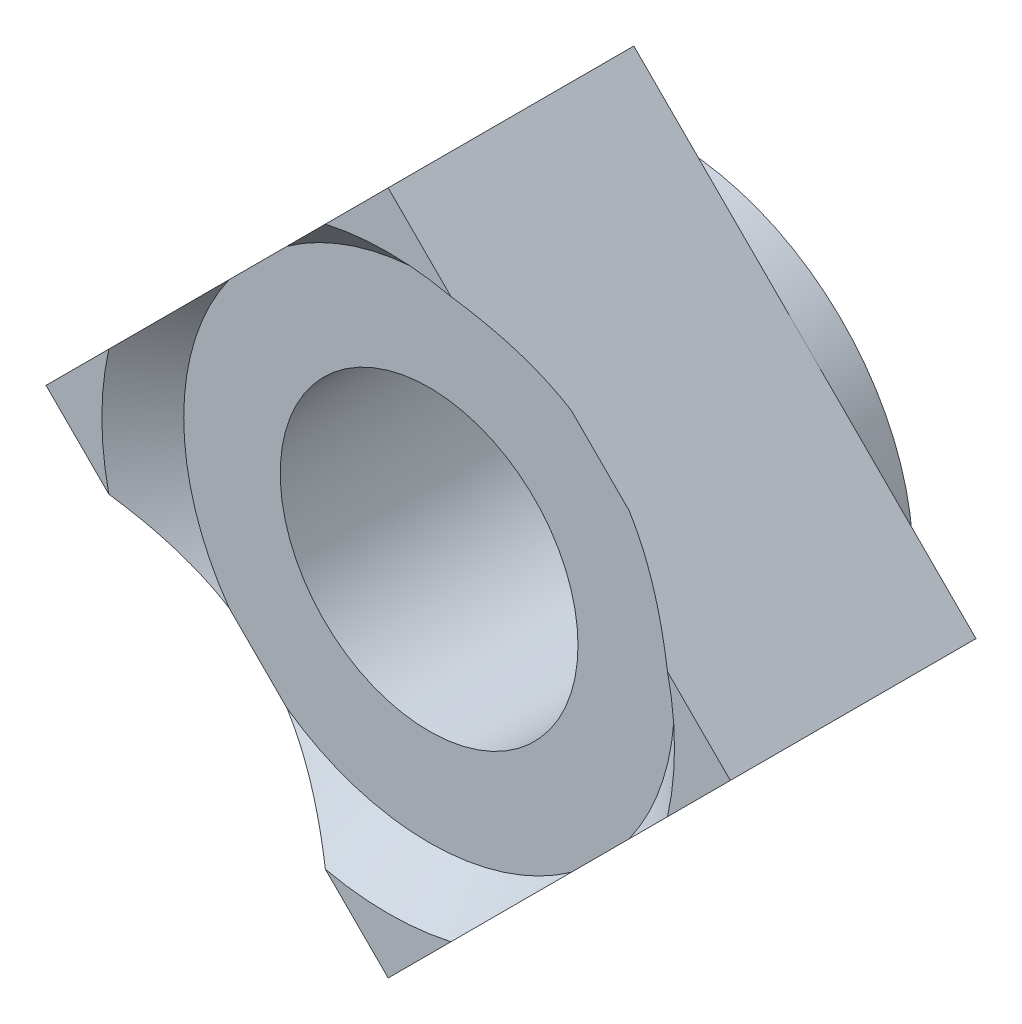
SolidWorks part; units mm, degrees
ref_plane "前视基准面" through (0, 0, 0) normal (0, 0, 1) x (1, 0, 0)
ref_plane "上视基准面" through (0, 0, 0) normal (0, 1, 0) x (1, 0, 0)
ref_plane "右视基准面" through (0, 0, 0) normal (1, 0, 0) x (0, 0, -1)
sketch "草图1" plane through (0, 0, 0) normal (0, 0, 1) x (1, 0, 0)
  circle A0 centre (0, 0) radius 6.5
  dimension "s" = 13
extrude "拉伸1" add sketch "草图1" along normal blind 1
sketch "草图2" plane through (0, 0, 1) normal (0, 0, 1) x (1, 0, 0)
  line L0 (0, 9.1924) -> (-9.1924, 0)
  line L1 (-9.1924, 0) -> (0, -9.1924)
  line L2 (0, -9.1924) -> (9.1924, 0)
  line L3 (9.1924, 0) -> (0, 9.1924)
  line L4 (0, 0) -> (6.5, 0) construction
  circle A0 centre (0, 0) radius 6.5 construction
  dimension "m" = 6.5
extrude "拉伸2" add sketch "草图2" along normal blind 5.5
sketch "草图3" plane through (0, 0, 6.5) normal (0, 0, 1) x (1, 0, 0)
  line L4 (9.1924, 0) -> (0, 9.1924)
  line L5 (0, 9.1924) -> (-9.1924, 0)
  line L6 (-9.1924, 0) -> (0, -9.1924)
  line L7 (0, -9.1924) -> (9.1924, 0)
  line L8 (9.1924, 0) -> (0, 9.1924)
  line L9 (0, 9.1924) -> (-9.1924, 0)
  line L10 (-9.1924, 0) -> (0, -9.1924)
  line L11 (0, -9.1924) -> (9.1924, 0)
  dimension "D1" = 0
extrude "拉伸3" add sketch "草图3" along normal blind 1.1
sketch "草图4" plane through (0, 0, 0) normal (1, 0, 0) x (0, 0, -1)
  line L0 (-6.5, 6.5924) -> (-6.5, 0)
  line L1 (-6.5, 6.5924) -> (-7.6, 7.6924)
  line L2 (-7.6, 7.6924) -> (-7.6, 0)
  line L3 (-7.6, 0) -> (-7.6, 9.1924) construction
  line L4 (-6.5, 9.1924) -> (-6.5, 0) construction
  line L5 (0, 0) -> (-8.9577, 0) construction
  line L6 (-6.5, 0) -> (-6.5, -9.1924) construction
  line L7 (-6.5, 0) -> (-7.6, 0)
  dimension "D1" = 45
  dimension "b" = 1.5
revolve "切除-旋转1" cut sketch "草图4" angle 360 about L5
sketch "草图5" plane through (0, 0, 6.5) normal (0, 0, 1) x (1, 0, 0)
  circle A0 centre (0, 0) radius 4
  dimension "dm" = 8
extrude "切除-拉伸1" cut sketch "草图5" against normal through all
sketch "草图6" plane through (0, 0, 0) normal (0, 0, -1) x (-1, 0, 0)
  circle A0 centre (0, 0) radius 5.11
  dimension "d3" = 10.22
extrude "切除-拉伸2" cut sketch "草图6" against normal blind 0.2
equation "\"D1@拉伸2\" = \"m@草图2\"-1"
